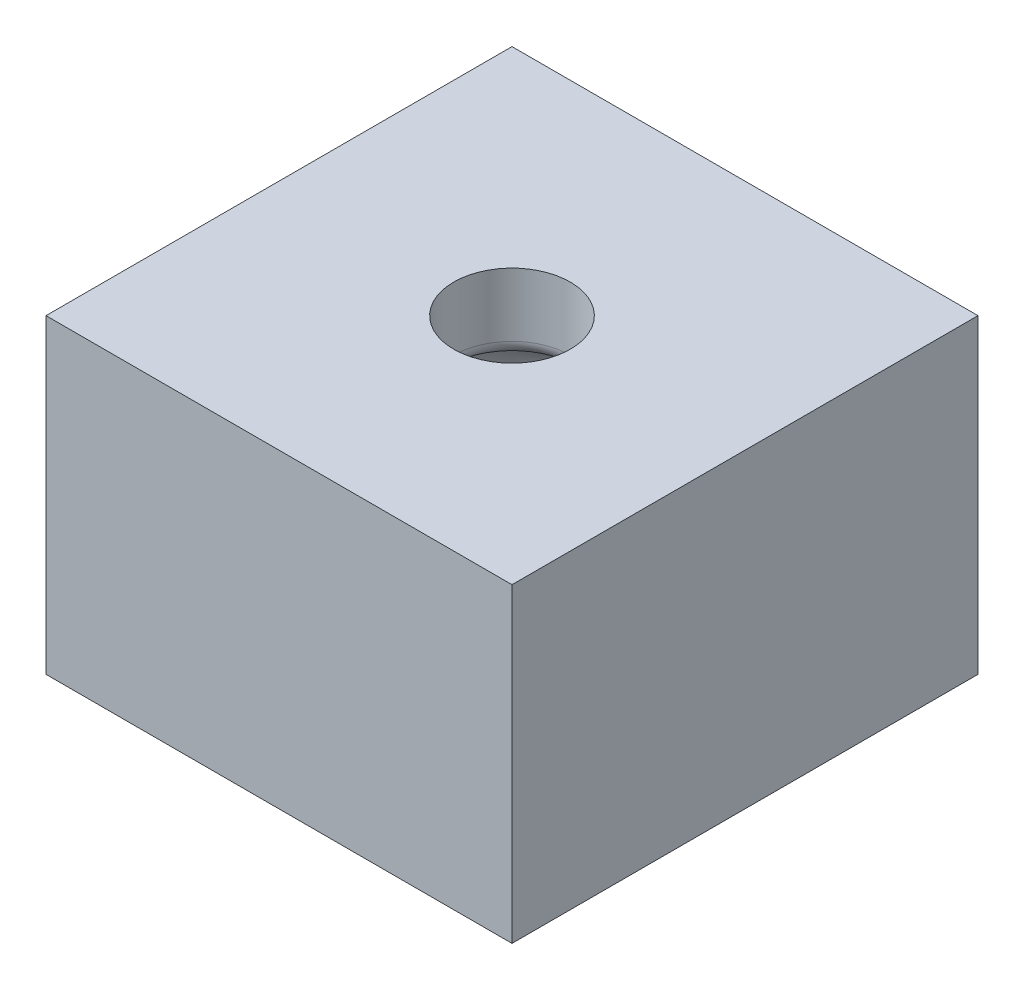
SolidWorks part; units mm, degrees
ref_plane "Front Plane" through (0, 0, 0) normal (0, 0, 1) x (1, 0, 0)
ref_plane "Top Plane" through (0, 0, 0) normal (0, 1, 0) x (1, 0, 0)
ref_plane "Right Plane" through (0, 0, 0) normal (1, 0, 0) x (0, 0, -1)
sketch "Sketch1" plane through (0, 0, 0) normal (0, 1, 0) x (1, 0, 0)
  line L1 (-76.2, -76.2) -> (76.2, -76.2)
  line L2 (-76.2, -76.2) -> (-76.2, 76.2)
  line L3 (-76.2, 76.2) -> (76.2, 76.2)
  line L4 (76.2, -76.2) -> (76.2, 76.2)
  line L5 (-76.2, -76.2) -> (76.2, 76.2) construction
  line L6 (-76.2, 76.2) -> (76.2, -76.2) construction
  point P0 (0, 0)
  dimension "D1" = 152.4
  dimension "D2" = 152.4
extrude "Boss-Extrude1" add sketch "Sketch1" along normal blind 101.6
sketch "Sketch3" plane through (0, 0, 0) normal (0, 0, 1) x (1, 0, 0)
  line L1 (-19.05, 101.6) -> (0, 101.6) construction
  line L10 (-19.05, 80.8537) -> (-19.05, 101.6)
  line L15 (-76.2, 101.6) -> (76.2, 101.6) construction
  line L17 (-19.05, 101.6) -> (-19.05, 76.2) construction
  line L22 (-19.05, 25.4) -> (0, 25.4) construction
  line L23 (-19.05, 101.6) -> (0, 101.6)
  line L24 (-76.2, 101.6) -> (-76.2, 0) construction
  line L25 (-19.05, 25.4) -> (0, 25.4)
  line L26 (0, 101.6) -> (0, 25.4)
  arc A4 (-19.05, 76.2) -> (-19.05, 25.4) centre (-19.05, 50.8) ccw construction
  arc A6 (-23.2833, 75.8447) -> (-19.05, 80.8537) centre (-24.13, 80.8537) ccw
  arc A7 (-19.05, 25.4) -> (-23.2833, 75.8447) centre (-19.05, 50.8) cw
  point P1 (0, 0)
  point P10 (0, 0)
  point P11 (0, 0)
  point P12 (-32.492, 152.4)
  point P13 (0, 0)
  point P15 (0, 0)
  dimension "D3" = 25.4
  dimension "D4" = 5.08
  dimension "D1" = 76.2
  dimension "D2" = 19.05
  dimension "D5" = 76.2
revolve "Cut-Revolve4" cut sketch "Sketch3" angle 360 about L26
